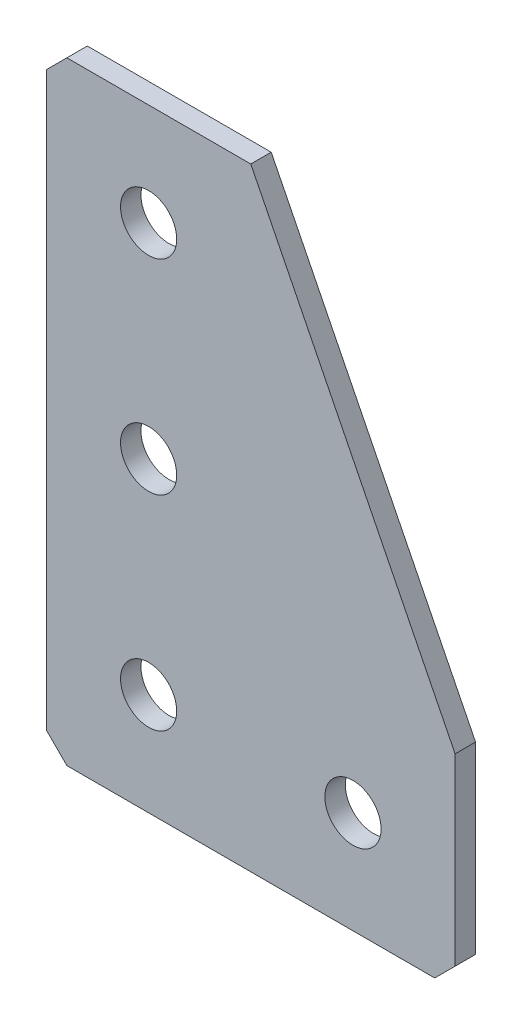
SolidWorks part; units mm, degrees
material "Простая углеродистая сталь"
ref_plane "Спереди(Плоскость XY)" through (0, 0, 0) normal (0, 0, 1) x (1, 0, 0)
ref_plane "Сверху(Плоскость XZ)" through (0, 0, 0) normal (0, 1, 0) x (1, 0, 0)
ref_plane "Справа(Плоскость ZY)" through (0, 0, 0) normal (1, 0, 0) x (0, 0, -1)
sketch "Эскиз1" plane through (0, 0, 0) normal (0, 0, -1) x (1, 0, 0)
  line L0 (0, 0) -> (0, 60)
  line L1 (0, 60) -> (40, 60)
  line L2 (40, 60) -> (40, 40)
  line L3 (40, 40) -> (20, 40) construction
  line L4 (20, 40) -> (20, 0) construction
  line L5 (20, 0) -> (0, 0)
  line L6 (40, 40) -> (20, 0)
  dimension "D1" = 60
  dimension "D2" = 20
  dimension "D3" = 20
  dimension "D4" = 20
extrude "Бобышка-Вытянуть1" add sketch "Эскиз1" along normal blind 2
hole_wizard "Отверстие с зазором M51" positions "Эскиз2" profile "Эскиз3" hole size "M5" standard "DIN" end condition through all
sketch "Эскиз2" plane through (0, 0, -2) normal (0, 0, -1) x (1, 0, 0)
  line L0 (10, 0) -> (10, 60) construction
  line L1 (0, 0) -> (20, 0) construction
  line L2 (40, 60) -> (0, 60) construction
  line L3 (40, 50) -> (0, 50) construction
  line L4 (40, 40) -> (40, 60) construction
  line L5 (0, 60) -> (0, 0) construction
  point P0 (30, 50)
  point P2 (10, 50)
  point P4 (10, 30)
  point P6 (10, 10)
  dimension "D1" = 20
  dimension "D2" = 20
  dimension "D3" = 20
  dimension "D4" = 10
sketch "Эскиз3" plane through (30, -50, -2) normal (1, 0, 0) x (0, 1, 0)
  line L0 (0, 0) -> (0, 2)
  line L1 (0, 2) -> (2.75, 2)
  line L2 (2.75, 2) -> (2.75, 0)
  line L5 (2.75, 0) -> (0, 0)
  line L11 (0, -6.35) -> (0, 107.95) construction
  dimension "Диаметр сквозного отверстия" = 5.5
  dimension "Глубина сквозного отверстия" = 2
chamfer "Фаска1" distance 2 angle 45 3 edges at (0, 0, -1) (40, -60, -1) (0, -60, -1)
